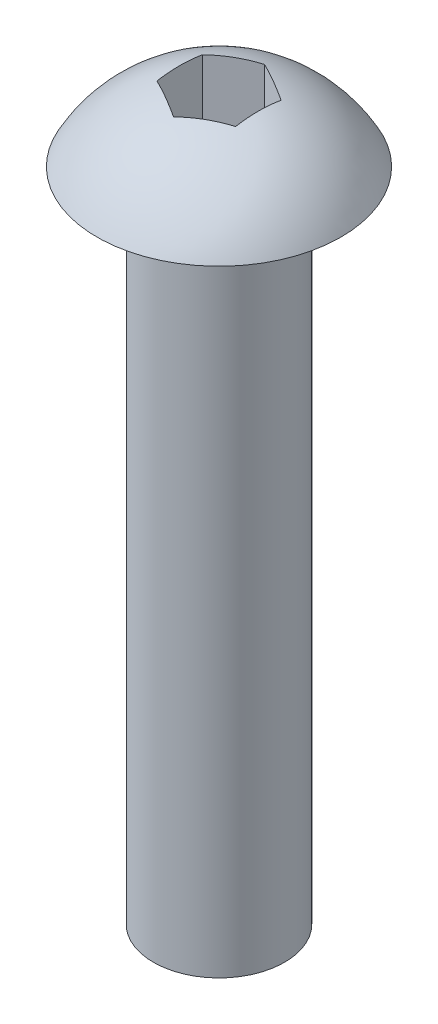
SolidWorks part; units mm, degrees
ref_plane "Front Plane" through (0, 0, 0) normal (0, 0, 1) x (1, 0, 0)
ref_plane "Top Plane" through (0, 0, 0) normal (0, 1, 0) x (1, 0, 0)
ref_plane "Right Plane" through (0, 0, 0) normal (1, 0, 0) x (0, 0, -1)
sketch "Sketch1" plane through (0, 0, 0) normal (0, 0, 1) x (1, 0, 0)
  line L0 (0, 0) -> (0, -25)
  line L1 (0, -25) -> (2.5, -25)
  line L2 (2.5, -25) -> (2.5, 0)
  line L3 (2.5, 0) -> (4.65, 0)
  line L4 (0, 0) -> (0, 2.8)
  arc A0 (0, 2.8) -> (4.65, 0) centre (0, -2.4612) cw
  dimension "D1" = 4.65
  dimension "D2" = 2.8
  dimension "D3" = 2.5
  dimension "D4" = 25
revolve "Revolve1" add sketch "Sketch1" angle 360 about L0
sketch "Sketch2" plane through (0, 0, 0) normal (0, 1, 0) x (1, 0, 0)
  line L1 (0, 1.7321) -> (-1.5, 0.866)
  line L2 (-1.5, 0.866) -> (-1.5, -0.866)
  line L3 (-1.5, -0.866) -> (0, -1.7321)
  line L4 (0, -1.7321) -> (1.5, -0.866)
  line L5 (1.5, -0.866) -> (1.5, 0.866)
  line L6 (1.5, 0.866) -> (0, 1.7321)
  circle A0 centre (0, 0) radius 1.5 construction
  dimension "D1" = 3
extrude "Cut-Extrude1" cut sketch "Sketch2" along normal blind 10
